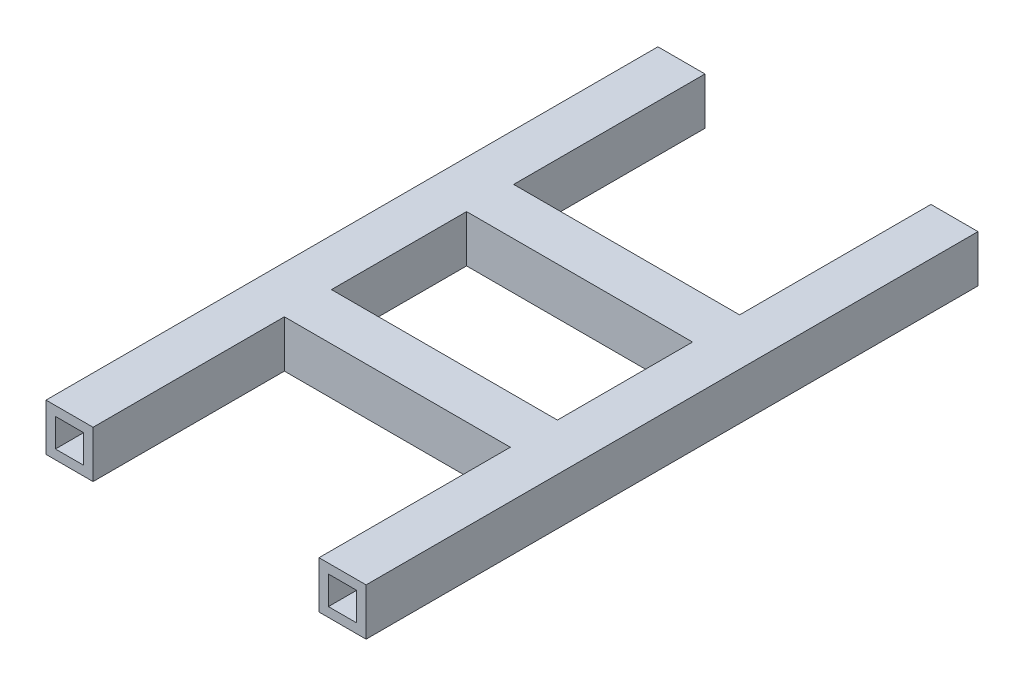
SolidWorks part; units mm, degrees
ref_plane "Front Plane" through (0, 0, 0) normal (0, 0, 1) x (1, 0, 0)
ref_plane "Top Plane" through (0, 0, 0) normal (0, 1, 0) x (1, 0, 0)
ref_plane "Right Plane" through (0, 0, 0) normal (1, 0, 0) x (0, 0, -1)
sketch "Sketch1" plane through (0, 0, 0) normal (0, 0, 1) x (1, 0, 0)
  line L0 (-25, 25) -> (25, 25)
  line L1 (-15, -15) -> (15, -15)
  line L2 (-15, -15) -> (-15, 15)
  line L3 (-15, 15) -> (15, 15)
  line L4 (15, -15) -> (15, 15)
  line L5 (-15, -15) -> (15, 15) construction
  line L6 (-15, 15) -> (15, -15) construction
  line L11 (25, -25) -> (25, 25)
  line L12 (-25, -25) -> (25, -25)
  line L13 (-25, -25) -> (-25, 25)
  line L14 (265, 25) -> (315, 25)
  line L15 (275, -15) -> (305, -15)
  line L16 (275, -15) -> (275, 15)
  line L17 (275, 15) -> (305, 15)
  line L18 (305, -15) -> (305, 15)
  line L19 (275, -15) -> (305, 15) construction
  line L20 (275, 15) -> (305, -15) construction
  line L21 (315, -25) -> (315, 25)
  line L22 (265, -25) -> (315, -25)
  line L23 (265, -25) -> (265, 25)
  point P0 (0, 0)
  point P10 (282.9842, -19.2284)
  dimension "D1" = 30
  dimension "D2" = 30
  dimension "D4" = 30
  dimension "D5" = 30
  dimension "D6" = 340
  dimension "D3" = 10
extrude "Boss-Extrude1" add sketch "Sketch1" along normal blind 650
sketch "Sketch2" plane through (0, -25, 0) normal (0, -1, 0) x (1, 0, 0)
  line L0 (265, 650) -> (315, 650) construction
  line L1 (265, 325) -> (315, 325) construction
  line L2 (265, 650) -> (265, 0) construction
  line L3 (315, 650) -> (315, 0) construction
  line L4 (25, 325) -> (265, 325) construction
  line L5 (25, 650) -> (25, 0) construction
  line L6 (145, 325) -> (145, 247.8157) construction
  circle A0 centre (290, 600) radius 10
  circle A2 centre (290, 550) radius 10
  circle A3 centre (290, 500) radius 10
  circle A4 centre (290, 150) radius 10
  circle A5 centre (290, 100) radius 10
  circle A6 centre (290, 50) radius 10
  circle A7 centre (0, 500) radius 10
  circle A8 centre (0, 550) radius 10
  circle A9 centre (0, 600) radius 10
  circle A10 centre (0, 50) radius 10
  circle A11 centre (0, 100) radius 10
  circle A12 centre (0, 150) radius 10
  dimension "D1" = 50
  dimension "D2" = 3
extrude "Cut-Extrude1" cut sketch "Sketch2" against normal blind 13 and the other way blind 18
sketch "Sketch3" plane through (265, 0, 0) normal (-1, 0, 0) x (0, 0, 1)
  line L0 (325, 25) -> (325, -25) construction
  line L1 (650, 25) -> (0, 25) construction
  line L2 (650, -25) -> (0, -25) construction
  line L3 (446.771, 25) -> (446.771, -25)
  line L4 (396.771, -25) -> (396.771, 25)
  line L5 (396.771, 25) -> (446.771, 25)
  line L6 (396.771, -25) -> (446.771, -25)
  line L7 (436.771, 15) -> (436.771, -15)
  line L8 (406.771, -15) -> (436.771, -15)
  line L9 (406.771, -15) -> (406.771, 15)
  line L10 (406.771, 15) -> (436.771, 15)
  line L11 (243.229, 15) -> (213.229, 15)
  line L12 (243.229, -15) -> (243.229, 15)
  line L13 (243.229, -15) -> (213.229, -15)
  line L14 (213.229, 15) -> (213.229, -15)
  line L15 (253.229, -25) -> (203.229, -25)
  line L16 (253.229, 25) -> (203.229, 25)
  line L17 (253.229, -25) -> (253.229, 25)
  line L18 (203.229, 25) -> (203.229, -25)
  dimension "D1" = 10
extrude "Boss-Extrude3" add sketch "Sketch3" along normal blind 240
ref_plane "Plane1" through (0, 0, 325) normal (0, 0, 1) x (1, 0, 0)
